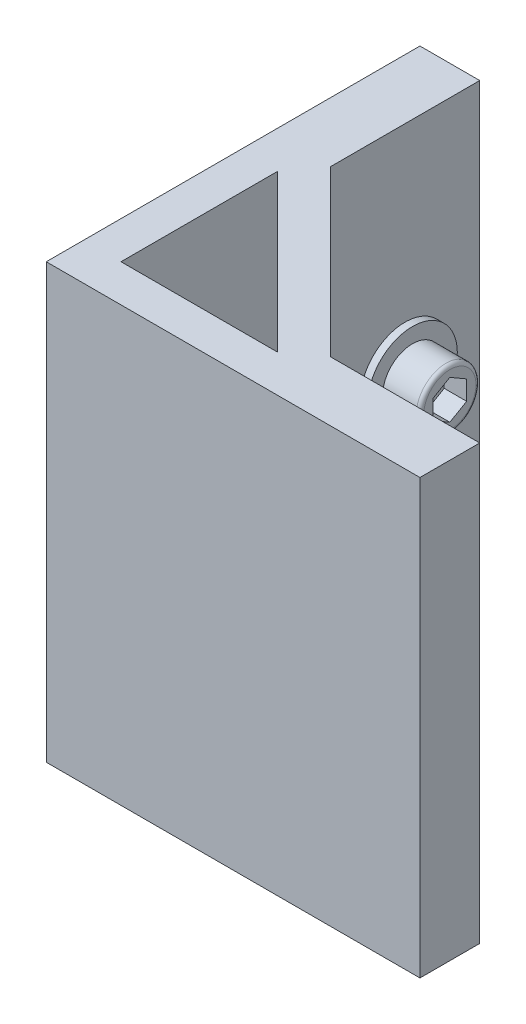
SolidWorks part; units mm, degrees
ref_plane "Front Plane" through (0, 0, 0) normal (0, 0, 1) x (1, 0, 0)
ref_plane "Top Plane" through (0, 0, 0) normal (0, 1, 0) x (1, 0, 0)
ref_plane "Right Plane" through (0, 0, 0) normal (1, 0, 0) x (0, 0, -1)
sketch "Sketch1" plane through (0, 0, 0) normal (0, 1, 0) x (1, 0, 0)
  line L0 (0, 50) -> (0, 0)
  line L1 (0, 0) -> (50, 0)
  line L2 (50, 0) -> (50, 8)
  line L3 (50, 8) -> (30, 8)
  line L4 (30, 8) -> (8, 30)
  line L5 (8, 30) -> (8, 50)
  line L6 (8, 50) -> (0, 50)
  line L7 (5, 25.9289) -> (25.9289, 5)
  line L8 (25.9289, 5) -> (5, 5)
  line L9 (5, 5) -> (5, 25.9289)
  point P10 (19, 19)
  dimension "D1" = 50
  dimension "D2" = 50
  dimension "D3" = 8
  dimension "D4" = 8
  dimension "D5" = 20
  dimension "D6" = 20
  dimension "D7" = 5
  dimension "D8" = 5
  dimension "D9" = 5
extrude "Boss-Extrude1" add sketch "Sketch1" along normal blind 58
sketch "Sketch2" plane through (8, 0, 0) normal (1, 0, 0) x (0, 0, -1)
  line L0 (40, 58) -> (40, 0) construction
  line L1 (30, 58) -> (50, 58) construction
  line L2 (30, 0) -> (50, 0) construction
  circle A0 centre (40, 29) radius 6
  dimension "D1" = 12
extrude "Boss-Extrude2" add sketch "Sketch2" along normal blind 1
sketch "Sketch3" plane through (9, 0, 0) normal (1, 0, 0) x (0, 0, -1)
  circle A0 centre (40, 29) radius 4
  dimension "D1" = 8
extrude "Boss-Extrude3" add sketch "Sketch3" along normal blind 5
sketch "Sketch4" plane through (14, 0, 0) normal (1, 0, 0) x (0, 0, -1)
  line L1 (40, 26.4019) -> (42.25, 27.701)
  line L2 (42.25, 27.701) -> (42.25, 30.299)
  line L3 (42.25, 30.299) -> (40, 31.5981)
  line L4 (40, 31.5981) -> (37.75, 30.299)
  line L5 (37.75, 30.299) -> (37.75, 27.701)
  line L6 (37.75, 27.701) -> (40, 26.4019)
  circle A0 centre (40, 29) radius 2.25 construction
  dimension "D1" = 4.5
extrude "Cut-Extrude1" cut sketch "Sketch4" against normal blind 3
fillet "Fillet1" radius 0.5 1 edges at (14, 29, -44)
